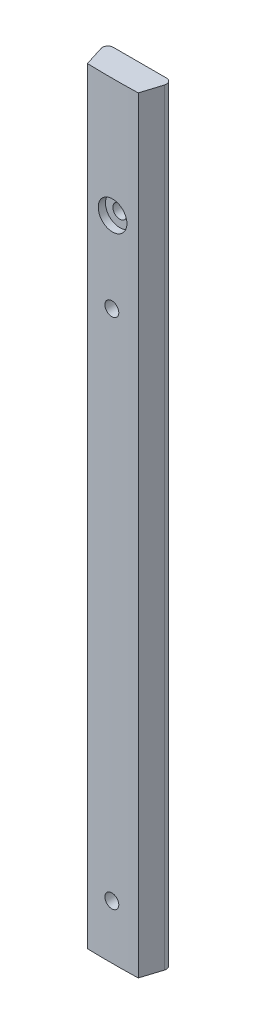
SolidWorks part; units mm, degrees
ref_plane "Front Plane" through (0, 0, 0) normal (0, 0, 1) x (1, 0, 0)
ref_plane "Top Plane" through (0, 0, 0) normal (0, 1, 0) x (1, 0, 0)
ref_plane "Right Plane" through (0, 0, 0) normal (1, 0, 0) x (0, 0, -1)
sketch "Sketch5" plane through (0, 0, 0) normal (0, 1, 0) x (1, 0, 0)
  line L0 (0, 0) -> (15.9512, 0)
  line L1 (15.9512, 0) -> (13.9573, -6.35)
  line L2 (13.9573, -6.35) -> (1.9939, -6.35) construction
  line L3 (1.9939, -6.35) -> (0, 0)
  line L4 (7.9756, 0) -> (7.9756, -6.35) construction
  arc A0 (13.9573, -6.35) -> (1.9939, -6.35) centre (7.9756, 196.7619) cw
  dimension "D1" = 15.9512
  dimension "D4" = 203.2
  dimension "D2" = 6.35
  dimension "D3" = 11.9634
extrude "Boss-Extrude4" add sketch "Sketch5" along normal blind 180.34
hole_wizard "CBORE for #4 Binding Head Machine Screw1" positions "Sketch6" profile "Sketch7" counterbore size "#4" standard "ANSI Inch" end condition through all
sketch "Sketch6" plane through (0, 0, 0) normal (0, 0, -1) x (-1, 0, 0)
  line L1 (-15.9512, 0) -> (0, 0) construction
  point P0 (-7.8271, 133.35)
  point P2 (-7.8271, 12.7)
  dimension "D1" = 133.35
  dimension "D2" = 12.7
sketch "Sketch7" plane through (7.8271, 133.35, 0) normal (1, 0, 0) x (0, 1, 0)
  line L0 (0, 0) -> (0, 6.4381)
  line L1 (0, 6.4381) -> (1.6319, 6.4381)
  line L3 (1.6319, 6.4381) -> (1.632, 1.7272)
  line L4 (1.632, 1.7272) -> (3.3731, 1.7272)
  line L5 (3.3731, 1.7272) -> (3.3731, 0)
  line L7 (3.3731, 0) -> (0, 0)
  line L11 (0, -6.35) -> (0, 107.95) construction
  dimension "Thru Hole Dia." = 3.2639
  dimension "Thru Hole Depth" = 6.4381
  dimension "C'Bore Dia." = 6.7462
  dimension "C'Bore Depth" = 1.7272
fillet "Fillet1" radius 1.27 2 edges at (0, 90.17, 0) (15.9512, 90.17, 0)
hole_wizard "CBORE for #4 Binding Head Machine Screw2" positions "3DSketch1" profile "Sketch8" counterbore size "#4" standard "ANSI Inch" end condition through all
sketch3d "3DSketch1"
  line L1 (7.9756, 0, 6.4381) -> (7.9756, 152.4245, 6.4381) construction
  arc A1 (1.9939, 0, 6.35) -> (13.9573, 0, 6.35) centre (7.9756, 0, -196.7619) ccw construction
  point P0 (7.9756, 152.4245, 6.4381)
  point P15 (7.9756, 203.2, -196.7619)
  dimension "D1" = 152.4245
sketch "Sketch8" plane through (7.9756, 152.4245, 6.4381) normal (1, 0, 0) x (0, -1, 0)
  line L0 (0, 0) -> (0, 6.4381)
  line L1 (0, 6.4381) -> (1.6319, 6.4381)
  line L3 (1.6319, 6.4381) -> (1.632, 1.7272)
  line L4 (1.632, 1.7272) -> (3.3731, 1.7272)
  line L5 (3.3731, 1.7272) -> (3.3731, 0)
  line L7 (3.3731, 0) -> (0, 0)
  line L11 (0, -6.35) -> (0, 107.95) construction
  dimension "Thru Hole Dia." = 3.2639
  dimension "Thru Hole Depth" = 6.4381
  dimension "C'Bore Dia." = 6.7462
  dimension "C'Bore Depth" = 1.7272
